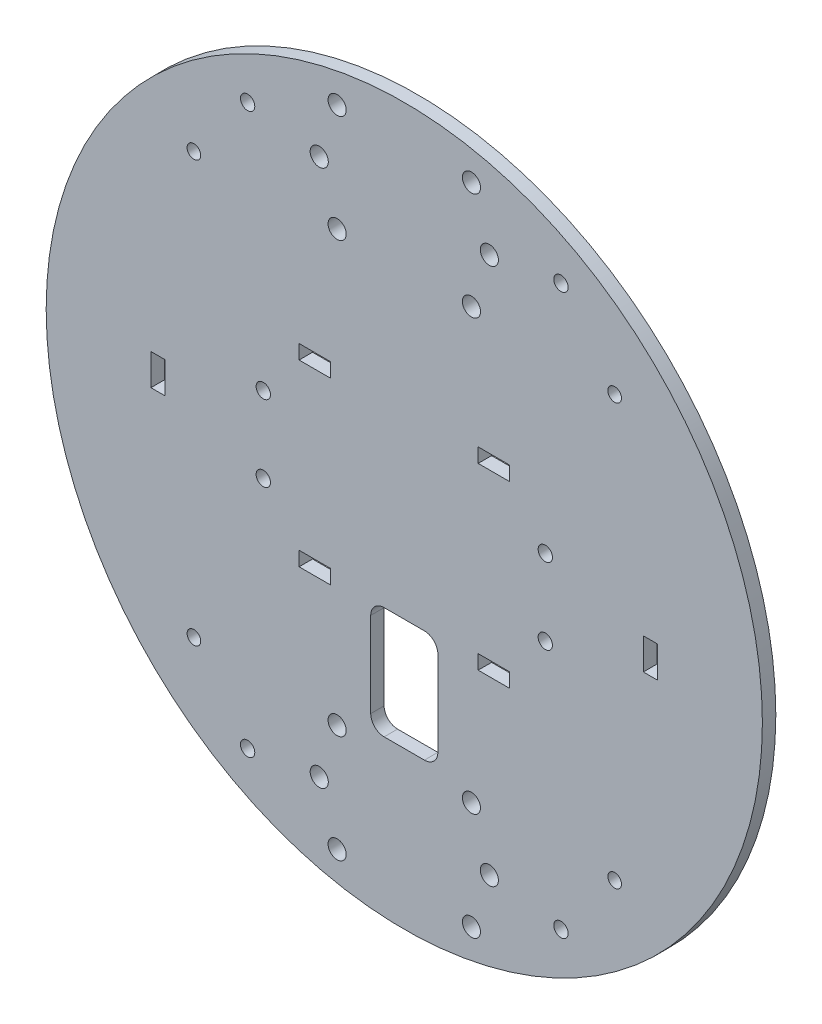
SolidWorks part; units mm, degrees
ref_plane "前视基准面" through (0, 0, 0) normal (0, 0, 1) x (1, 0, 0)
ref_plane "上视基准面" through (0, 0, 0) normal (0, 1, 0) x (1, 0, 0)
ref_plane "右视基准面" through (0, 0, 0) normal (1, 0, 0) x (0, 0, -1)
sketch "草图1" plane through (0, 0, 0) normal (0, 0, 1) x (1, 0, 0)
  line L0 (0, 0) -> (-47, 47) construction
  line L1 (50, 50) -> (-50, 50) construction
  line L2 (-50, 50) -> (-50, -50) construction
  line L3 (-50, -50) -> (50, -50) construction
  line L4 (50, -50) -> (50, 50) construction
  line L9 (-50, 50) -> (-47, 50) construction
  line L10 (-50, 50) -> (-50, 47) construction
  line L11 (-50, 47) -> (-47, 47) construction
  line L12 (-47, 50) -> (-47, 47) construction
  line L13 (0, 0) -> (47, 47) construction
  line L14 (0, 0) -> (0, 171.8985) construction
  line L15 (0, -45) -> (7.5, -45) construction
  line L16 (0, -45) -> (0, -50) construction
  line L17 (0, -50) -> (7.5, -50) construction
  line L18 (7.5, -45) -> (7.5, -50) construction
  line L19 (-7.5, -20) -> (7.5, -20)
  line L20 (-7.5, -20) -> (-7.5, -45)
  line L21 (-7.5, -45) -> (7.5, -45)
  line L22 (7.5, -20) -> (7.5, -45)
  line L25 (0, 60) -> (19, 60) construction
  line L26 (0, 0) -> (43.586, 0) construction
  line L27 (-15, 48) -> (15, 48) construction
  line L28 (-15, 48) -> (-15, 72) construction
  line L29 (-15, 72) -> (15, 72) construction
  line L30 (15, 48) -> (15, 72) construction
  line L31 (-15, 48) -> (15, 72) construction
  line L32 (-15, 72) -> (15, 48) construction
  line L34 (-35, -62.5) -> (35, -62.5) construction
  line L35 (-35, -62.5) -> (-35, 62.5) construction
  line L36 (-35, 62.5) -> (35, 62.5) construction
  line L37 (35, -62.5) -> (35, 62.5) construction
  line L38 (-35, -62.5) -> (35, 62.5) construction
  line L39 (-35, 62.5) -> (35, -62.5) construction
  line L40 (-31.5, -8.5) -> (31.5, -8.5) construction
  line L41 (-31.5, -8.5) -> (-31.5, 8.5) construction
  line L42 (-31.5, 8.5) -> (31.5, 8.5) construction
  line L43 (31.5, -8.5) -> (31.5, 8.5) construction
  line L44 (-31.5, -8.5) -> (31.5, 8.5) construction
  line L45 (-31.5, 8.5) -> (31.5, -8.5) construction
  circle A0 centre (0, 0) radius 80
  circle A2 centre (-47, 47) radius 1.52
  circle A3 centre (0, 0) radius 50 construction
  circle A4 centre (47, 47) radius 1.52
  circle A5 centre (47, -47) radius 1.52
  circle A6 centre (-47, -47) radius 1.52
  circle A7 centre (19, 60) radius 2.025
  circle A8 centre (15, 72) radius 2.025
  circle A9 centre (15, 48) radius 2.025
  circle A10 centre (-15, 48) radius 2.025
  circle A11 centre (-19, 60) radius 2.025
  circle A12 centre (-15, 72) radius 2.025
  circle A13 centre (15, -48) radius 2.025
  circle A14 centre (15, -72) radius 2.025
  circle A15 centre (19, -60) radius 2.025
  circle A16 centre (-15, -48) radius 2.025
  circle A17 centre (-19, -60) radius 2.025
  circle A18 centre (-15, -72) radius 2.025
  circle A19 centre (-35, 62.5) radius 1.6
  circle A20 centre (-35, -62.5) radius 1.6
  circle A21 centre (-31.5, 8.5) radius 1.6
  circle A22 centre (-31.5, -8.5) radius 1.6
  circle A23 centre (31.5, -8.5) radius 1.6
  circle A24 centre (31.5, 8.5) radius 1.6
  circle A25 centre (35, 62.5) radius 1.6
  circle A26 centre (35, -62.5) radius 1.6
  point P11 (0, -50)
  point P29 (0, 60)
  dimension "D1" = 160
  dimension "D2" = 100
  dimension "D5" = 3.04
  dimension "D14" = 4.05
  dimension "D17" = 4.05
  dimension "D18" = 4.05
  dimension "D21" = 3.2
  dimension "D22" = 3.2
  dimension "D25" = 3.2
  dimension "D26" = 3.2
  dimension "D3" = 3
  dimension "D4" = 3
  dimension "D6" = 4
  dimension "D7" = 90
  dimension "D8" = 5
  dimension "D9" = 7.5
  dimension "D10" = 15
  dimension "D11" = 25
  dimension "D12" = 60
  dimension "D13" = 19
  dimension "D15" = 30
  dimension "D16" = 24
  dimension "D19" = 70
  dimension "D20" = 125
  dimension "D23" = 63
  dimension "D24" = 17
extrude "凸台-拉伸1" add sketch "草图1" along normal blind 3
sketch "电池扎带草图" plane through (0, 0, 0) normal (0, 0, 1) x (1, 0, 0)
  line L0 (0, 0) -> (55, 0) construction
  line L1 (-20, -20) -> (20, -20) construction
  line L2 (-20, -20) -> (-20, 20) construction
  line L3 (-20, 20) -> (20, 20) construction
  line L4 (20, -20) -> (20, 20) construction
  line L5 (-20, -20) -> (20, 20) construction
  line L6 (-20, 20) -> (20, -20) construction
  line L7 (16.5, -18.4) -> (23.5, -18.4)
  line L8 (16.5, 18.4) -> (23.5, 18.4)
  line L9 (16.5, 18.4) -> (16.5, 21.6)
  line L10 (16.5, 21.6) -> (23.5, 21.6)
  line L11 (23.5, 18.4) -> (23.5, 21.6)
  line L12 (16.5, 18.4) -> (23.5, 21.6) construction
  line L13 (16.5, 21.6) -> (23.5, 18.4) construction
  line L14 (16.5, -18.4) -> (16.5, -21.6)
  line L15 (16.5, -21.6) -> (23.5, -21.6)
  line L16 (23.5, -18.4) -> (23.5, -21.6)
  line L17 (0, 0) -> (0, -16.0006) construction
  line L18 (53.4, 3.5) -> (56.6, 3.5)
  line L19 (53.4, 3.5) -> (53.4, -3.5)
  line L20 (53.4, -3.5) -> (56.6, -3.5)
  line L21 (56.6, 3.5) -> (56.6, -3.5)
  line L22 (53.4, 3.5) -> (56.6, -3.5) construction
  line L23 (53.4, -3.5) -> (56.6, 3.5) construction
  line L24 (-16.5, 21.6) -> (-23.5, 21.6)
  line L25 (-23.5, 18.4) -> (-23.5, 21.6)
  line L26 (-16.5, 18.4) -> (-23.5, 18.4)
  line L27 (-16.5, 18.4) -> (-16.5, 21.6)
  line L28 (-53.4, -3.5) -> (-56.6, -3.5)
  line L29 (-56.6, 3.5) -> (-56.6, -3.5)
  line L30 (-53.4, 3.5) -> (-56.6, 3.5)
  line L31 (-53.4, 3.5) -> (-53.4, -3.5)
  line L32 (-16.5, -18.4) -> (-16.5, -21.6)
  line L33 (-16.5, -21.6) -> (-23.5, -21.6)
  line L34 (-23.5, -18.4) -> (-23.5, -21.6)
  line L35 (-16.5, -18.4) -> (-23.5, -18.4)
  line L36 (0, 55) -> (0, 0) construction
  line L45 (-12, 75.25) -> (12, 75.25) construction
  line L46 (-12, 75.25) -> (-12, 34.75) construction
  line L47 (-12, 34.75) -> (12, 34.75) construction
  line L48 (12, 75.25) -> (12, 34.75) construction
  line L49 (-12, 75.25) -> (12, 34.75) construction
  line L50 (-12, 34.75) -> (12, 75.25) construction
  point P0 (0, 0)
  point P48 (0, 55)
  dimension "D1" = 40
  dimension "D2" = 40
  dimension "D3" = 55
  dimension "D4" = 7
  dimension "D5" = 3.2
  dimension "D6" = 3.2
  dimension "D7" = 7
  dimension "D10" = 55
  dimension "D11" = 24
  dimension "D12" = 40.5
extrude "电池+BB响扎带孔位" cut sketch "电池扎带草图" along normal blind 3
fillet "圆角1" radius 3 4 edges at (-7.5, -45, 1.5) (7.5, -45, 1.5) (-7.5, -20, 1.5) (7.5, -20, 1.5)
